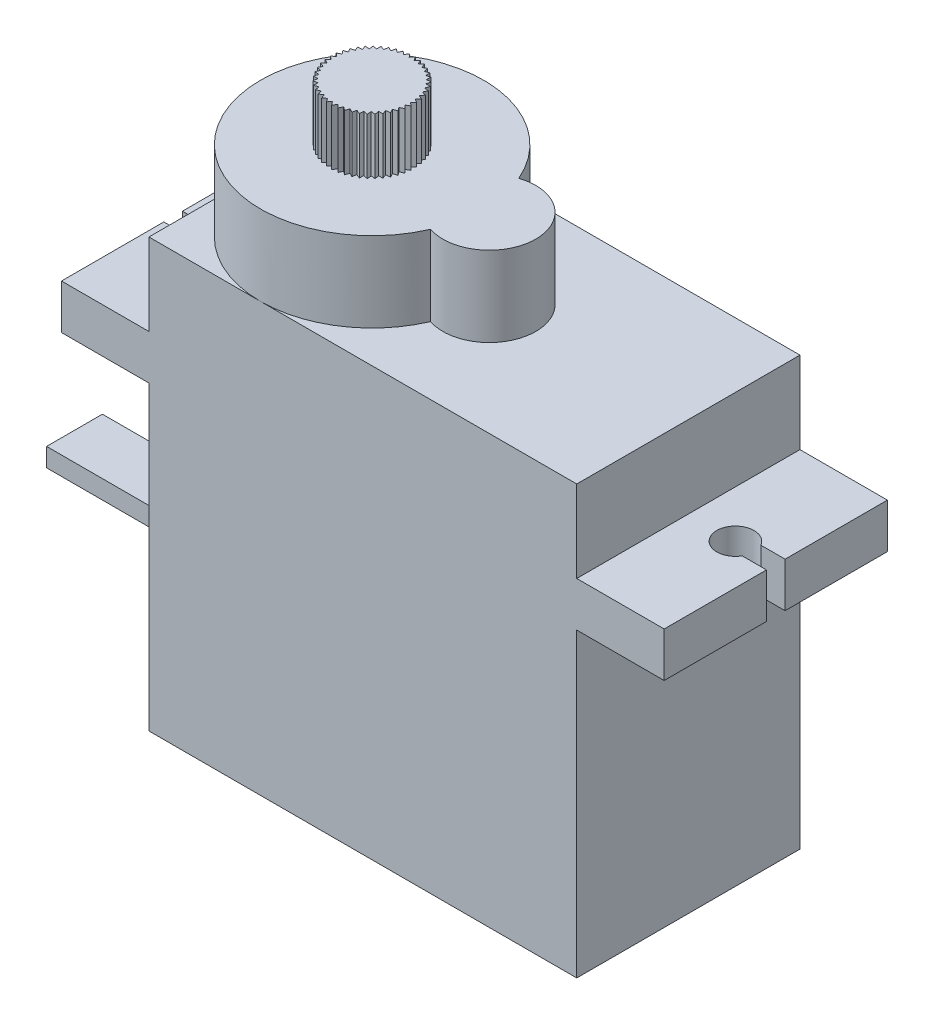
SolidWorks part; units mm, degrees
ref_plane "Front Plane" through (0, 0, 0) normal (0, 0, 1) x (1, 0, 0)
ref_plane "Top Plane" through (0, 0, 0) normal (0, 1, 0) x (1, 0, 0)
ref_plane "Right Plane" through (0, 0, 0) normal (1, 0, 0) x (0, 0, -1)
sketch "Sketch2" plane through (0, 0, 0) normal (0, 1, 0) x (1, 0, 0)
  line L1 (-11.5, -6) -> (11.5, -6)
  line L2 (-11.5, -6) -> (-11.5, 6)
  line L3 (-11.5, 6) -> (11.5, 6)
  line L4 (11.5, -6) -> (11.5, 6)
  line L5 (-11.5, -6) -> (11.5, 6) construction
  line L6 (-11.5, 6) -> (11.5, -6) construction
  point P0 (0, 0)
  dimension "D1" = 12
  dimension "D2" = 23
extrude "Boss-Extrude1" add sketch "Sketch2" against normal blind 23
sketch "Sketch3" plane through (0, 0, 0) normal (0, 1, 0) x (1, 0, 0)
  line L0 (11.5, 6) -> (-11.5, 6) construction
  line L1 (-16.2, -6) -> (16.2, -6)
  line L2 (-16.2, -6) -> (-16.2, 6)
  line L3 (-16.2, 6) -> (16.2, 6)
  line L4 (16.2, -6) -> (16.2, 6)
  line L5 (-16.2, -6) -> (16.2, 6) construction
  line L6 (-16.2, 6) -> (16.2, -6) construction
  line L8 (-15.5843, 0.5) -> (-16.2, 0.5)
  line L9 (-15.5843, 0.5) -> (-15.5843, -0.5)
  line L10 (-15.5843, -0.5) -> (-16.2, -0.5)
  line L11 (-16.2, 0.5) -> (-16.2, -0.5)
  line L12 (16.2, 0.5) -> (14.8944, 0.5)
  line L13 (16.2, 0.5) -> (16.2, -0.5)
  line L14 (16.2, -0.5) -> (14.8944, -0.5)
  line L15 (14.8944, 0.5) -> (14.8944, -0.5)
  circle A0 centre (-14.7183, 0) radius 1
  circle A1 centre (14.0284, 0) radius 1
  point P0 (0, 0)
  line M15 (11.5, -6) -> (11.5, 6)
  line M17 (-11.5, 6) -> (-11.5, -6)
  dimension "D2" = 2
  dimension "D1" = 32.4
  dimension "D3" = 1
  dimension "D4" = 1
extrude "Boss-Extrude2" add sketch "Sketch3" against normal blind 2.4 from offset 4.4 contours A0 L10 L2 L1 L3 L8 M17 | A1 L12 L4 L3 L1 L14 M15 offset against normal yes
sketch "Sketch4" plane through (0, 0, 0) normal (0, 1, 0) x (1, 0, 0)
  line L0 (-11.5, 6) -> (-11.5, -6) construction
  line L1 (11.5, 6) -> (-11.5, 6) construction
  line L2 (3.3, 0) -> (-11.5, 0) construction
  circle A0 centre (-5.5, 0) radius 6
  circle A1 centre (0.8, 0) radius 2.5
  dimension "D1" = 14.8
  dimension "D2" = 5
extrude "Boss-Extrude3" add sketch "Sketch4" along normal blind 4.3 contours L2 A1 A0 | A1 L2 A0 | A1 L2 A0 | L2 A1 A0 | L2 A0 A1 | A0 L2 A1
sketch "Sketch5" plane through (0, 4.3, 0) normal (0, 1, 0) x (1, 0, 0)
  line L0 (-3.255, -0.15) -> (-3.4372, 0)
  line L1 (-3.4372, 0) -> (-3.255, 0.15)
  line L2 (-3.295, -0.4479) -> (-3.4556, -0.2749)
  line L3 (-3.4556, -0.2749) -> (-3.255, -0.1506)
  line L4 (-3.3744, -0.7378) -> (-3.5105, -0.545)
  line L5 (-3.5105, -0.545) -> (-3.2951, -0.4484)
  line L6 (-3.4917, -1.0145) -> (-3.6009, -0.8053)
  line L7 (-3.6009, -0.8053) -> (-3.3746, -0.7383)
  line L8 (-3.6448, -1.2731) -> (-3.7252, -1.0512)
  line L9 (-3.7252, -1.0512) -> (-3.492, -1.015)
  line L10 (-3.8311, -1.5091) -> (-3.8811, -1.2784)
  line L11 (-3.8811, -1.2784) -> (-3.6452, -1.2736)
  line L12 (-4.0471, -1.718) -> (-4.0659, -1.4828)
  line L13 (-4.0659, -1.4828) -> (-3.8315, -1.5095)
  line L14 (-4.2891, -1.8964) -> (-4.2764, -1.6607)
  line L15 (-4.2764, -1.6607) -> (-4.0476, -1.7184)
  line L16 (-4.5526, -2.0408) -> (-4.5086, -1.809)
  line L17 (-4.5086, -1.809) -> (-4.2896, -1.8967)
  line L18 (-4.8331, -2.1489) -> (-4.7586, -1.925)
  line L19 (-4.7586, -1.925) -> (-4.5532, -2.0411)
  line L20 (-5.1255, -2.2186) -> (-5.0218, -2.0066)
  line L21 (-5.0218, -2.0066) -> (-4.8337, -2.1491)
  line L22 (-5.4245, -2.2487) -> (-5.2935, -2.0525)
  line L23 (-5.2935, -2.0525) -> (-5.126, -2.2187)
  line L24 (-5.7249, -2.2387) -> (-5.5689, -2.0617)
  line L25 (-5.5689, -2.0617) -> (-5.4251, -2.2488)
  line L26 (-6.0213, -2.1888) -> (-5.8431, -2.0341)
  line L27 (-5.8431, -2.0341) -> (-5.7255, -2.2387)
  line L28 (-6.3084, -2.0998) -> (-6.1112, -1.9702)
  line L29 (-6.1112, -1.9702) -> (-6.0219, -2.1886)
  line L30 (-6.5811, -1.9733) -> (-6.3683, -1.8712)
  line L31 (-6.3683, -1.8712) -> (-6.3089, -2.0996)
  line L32 (-6.8344, -1.8116) -> (-6.61, -1.7387)
  line L33 (-6.61, -1.7387) -> (-6.5816, -1.973)
  line L34 (-7.064, -1.6176) -> (-6.8318, -1.5753)
  line L35 (-6.8318, -1.5753) -> (-6.8349, -1.8112)
  line L36 (-7.2656, -1.3947) -> (-7.0299, -1.3837)
  line L37 (-7.0299, -1.3837) -> (-7.0644, -1.6172)
  line L38 (-7.4358, -1.1469) -> (-7.2007, -1.1674)
  line L39 (-7.2007, -1.1674) -> (-7.266, -1.3942)
  line L40 (-7.5714, -0.8786) -> (-7.3411, -0.9304)
  line L41 (-7.3411, -0.9304) -> (-7.436, -1.1464)
  line L42 (-7.67, -0.5947) -> (-7.4487, -0.6767)
  line L43 (-7.4487, -0.6767) -> (-7.5716, -0.8781)
  line L44 (-7.7299, -0.3002) -> (-7.5215, -0.4109)
  line L45 (-7.5215, -0.4109) -> (-7.6701, -0.5942)
  line L46 (-7.75, -0.0003) -> (-7.5582, -0.1378)
  line L47 (-7.5582, -0.1378) -> (-7.73, -0.2996)
  line L48 (-7.73, 0.2996) -> (-7.5582, 0.1378)
  line L49 (-7.5582, 0.1378) -> (-7.75, 0.0003)
  line L50 (-7.6701, 0.5942) -> (-7.5215, 0.4109)
  line L51 (-7.5215, 0.4109) -> (-7.7299, 0.3002)
  line L52 (-7.5716, 0.8781) -> (-7.4487, 0.6767)
  line L53 (-7.4487, 0.6767) -> (-7.67, 0.5947)
  line L54 (-7.436, 1.1464) -> (-7.3411, 0.9304)
  line L55 (-7.3411, 0.9304) -> (-7.5714, 0.8786)
  line L56 (-7.266, 1.3942) -> (-7.2007, 1.1674)
  line L57 (-7.2007, 1.1674) -> (-7.4358, 1.1469)
  line L58 (-7.0644, 1.6172) -> (-7.0299, 1.3837)
  line L59 (-7.0299, 1.3837) -> (-7.2656, 1.3947)
  line L60 (-6.8349, 1.8112) -> (-6.8318, 1.5753)
  line L61 (-6.8318, 1.5753) -> (-7.064, 1.6176)
  line L62 (-6.5816, 1.973) -> (-6.61, 1.7387)
  line L63 (-6.61, 1.7387) -> (-6.8344, 1.8116)
  line L64 (-6.3089, 2.0996) -> (-6.3683, 1.8712)
  line L65 (-6.3683, 1.8712) -> (-6.5811, 1.9733)
  line L66 (-6.0219, 2.1886) -> (-6.1112, 1.9702)
  line L67 (-6.1112, 1.9702) -> (-6.3084, 2.0998)
  line L68 (-5.7255, 2.2387) -> (-5.8431, 2.0341)
  line L69 (-5.8431, 2.0341) -> (-6.0213, 2.1888)
  line L70 (-5.4251, 2.2488) -> (-5.5689, 2.0617)
  line L71 (-5.5689, 2.0617) -> (-5.7249, 2.2387)
  line L72 (-5.126, 2.2187) -> (-5.2935, 2.0525)
  line L73 (-5.2935, 2.0525) -> (-5.4245, 2.2487)
  line L74 (-4.8337, 2.1491) -> (-5.0218, 2.0066)
  line L75 (-5.0218, 2.0066) -> (-5.1255, 2.2186)
  line L76 (-4.5532, 2.0411) -> (-4.7586, 1.925)
  line L77 (-4.7586, 1.925) -> (-4.8331, 2.1489)
  line L78 (-4.2896, 1.8967) -> (-4.5086, 1.809)
  line L79 (-4.5086, 1.809) -> (-4.5526, 2.0408)
  line L80 (-4.0476, 1.7184) -> (-4.2764, 1.6607)
  line L81 (-4.2764, 1.6607) -> (-4.2891, 1.8964)
  line L82 (-3.8315, 1.5095) -> (-4.0659, 1.4828)
  line L83 (-4.0659, 1.4828) -> (-4.0471, 1.718)
  line L84 (-3.6452, 1.2736) -> (-3.8811, 1.2784)
  line L85 (-3.8811, 1.2784) -> (-3.8311, 1.5091)
  line L86 (-3.492, 1.015) -> (-3.7252, 1.0512)
  line L87 (-3.7252, 1.0512) -> (-3.6448, 1.2731)
  line L88 (-3.3746, 0.7383) -> (-3.6009, 0.8053)
  line L89 (-3.6009, 0.8053) -> (-3.4917, 1.0145)
  line L90 (-3.2951, 0.4484) -> (-3.5105, 0.545)
  line L91 (-3.5105, 0.545) -> (-3.3744, 0.7378)
  line L92 (-3.255, 0.1506) -> (-3.4556, 0.2749)
  line L93 (-3.4556, 0.2749) -> (-3.295, 0.4479)
  circle A0 centre (-5.5, 0) radius 2.25
  point P146 (-5.5, 0)
  dimension "D1" = 4.5
  dimension "D2" = 0.15
  dimension "D3" = 47
extrude "Boss-Extrude4" add sketch "Sketch5" along normal blind 3 contours L25 A0 L22 L23 L20 L21 L18 L19 L16 L17 L14 L15 L12 L13 L10 L11 L8 L9 L6 L7 L4 L5 L2 L3 L0 L1 L92 L93 L90 L91 L88 L89 L86 L87 L84
sketch "Sketch6" plane through (-11.5, 0, 0) normal (-1, 0, 0) x (0, 0, 1)
  line L0 (-6, -23) -> (6, -23) construction
  line L1 (-1.5, -17) -> (1.5, -17)
  line L2 (-1.5, -17) -> (-1.5, -18)
  line L3 (-1.5, -18) -> (1.5, -18)
  line L4 (1.5, -17) -> (1.5, -18)
  point P7 (0, -17)
  dimension "D1" = 5
  dimension "D2" = 3
  dimension "D3" = 1
extrude "Boss-Extrude5" add sketch "Sketch6" along normal blind 10
